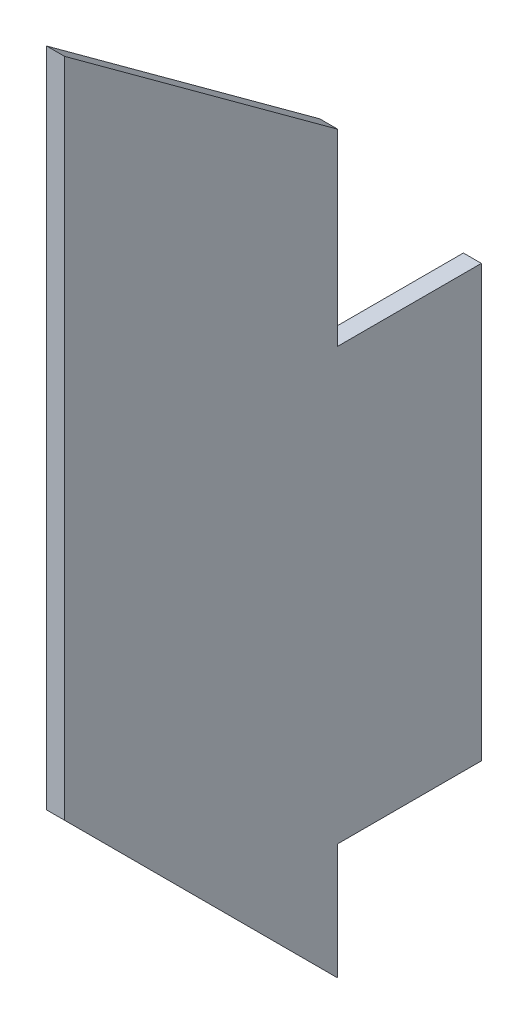
SolidWorks part; units mm, degrees
ref_plane "Front Plane" through (0, 0, 0) normal (1, 0, 0) x (0, 1, 0)
ref_plane "Top Plane" through (0, 0, 0) normal (0, 0, 1) x (0, 1, 0)
ref_plane "Right Plane" through (0, 0, 0) normal (0, 1, 0) x (-1, 0, 0)
sketch "Sketch2" plane through (0, 0, 0) normal (1, 0, 0) x (0, 1, 0)
  line L0 (0, 0) -> (48.3, 48.3)
  line L1 (0, 0) -> (20.55, 0)
  line L2 (48.3, 48.3) -> (165.3, 48.3)
  line L3 (165.3, 48.3) -> (130, 0)
  line L4 (20.55, 0) -> (20.55, -25.4)
  line L5 (20.55, -25.4) -> (96.75, -25.4)
  line L6 (96.75, -25.4) -> (96.75, 0)
  line L7 (96.75, 0) -> (130, 0)
  point P7 (0, 0)
  dimension "D1" = 48.3
  dimension "D2" = 130
  dimension "D3" = 117
  dimension "D4" = 45
  dimension "D5" = 76.2
  dimension "D6" = 25.4
  dimension "D7" = 20.55
  dimension "D8" = 33.25
extrude "Boss-Extrude1" add sketch "Sketch2" along normal blind 3.18
